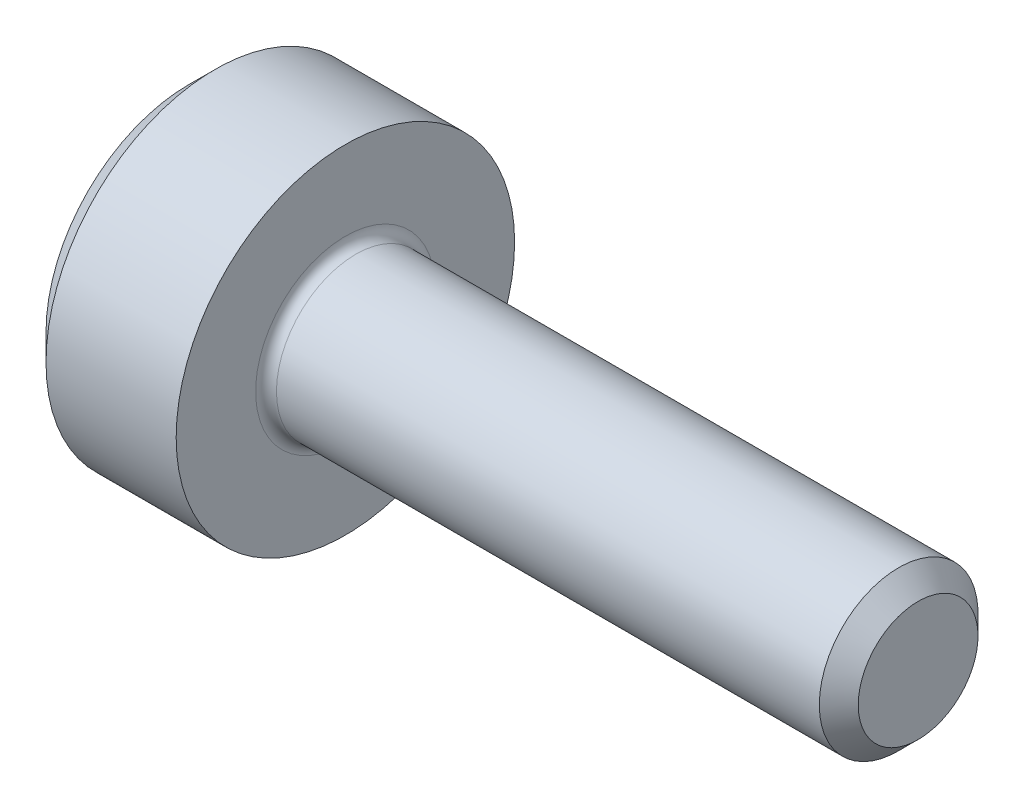
SolidWorks part; units mm, degrees
revolve "Base-Revolve" add sketch "BodySke"
sketch "BodySke" plane through (0, 0, 0) normal (0, 0, 1) x (1, 0, 0)
  line L0 (0, 0) -> (0, 2.75)
  line L1 (0.5, 3.25) -> (3, 3.25)
  line L2 (3, 3.25) -> (3, 1.524)
  line L3 (3, 1.524) -> (13.626, 1.524)
  line L4 (14, 1.15) -> (14, 0)
  line L5 (14, 0) -> (0, 0)
  line L6 (-31.75, 0) -> (127, 0) construction
  line L7 (0, 2.75) -> (0.5, 3.25)
  line L8 (14, 1.15) -> (13.626, 1.524)
  line L9 (0, -2.75) -> (0.5, -3.25) construction
  line L10 (14, -1.15) -> (13.626, -1.524) construction
  line L11 (3.8, 9.525) -> (3.8, 3.175) construction
  line L12 (6, 9.525) -> (6, 3.175) construction
  line L13 (-36, 9.525) -> (-36, 3.175) construction
  dimension "Diameter" = 3.048
  dimension "Head_ht" = 3
  dimension "Length" = 11
  dimension "Body_ch_ang" = 45
  dimension "Head_dia" = 6.5
  dimension "Head_ch_ang" = 45
  dimension "Minor_dia" = 2.3
  dimension "Advance" = 0.8
  dimension "Thread_nom" = 8
  dimension "Thread_length" = 50
  dimension "Head_ch_ht" = 0.5
cosmetic thread "ThreadCosmetic"
fillet "Fillet1" radius 0.2 1 edges at (3, 0, 1.524)
ref_plane "Plane1" through (0, 0, 0) normal (0, 0, 1) x (1, 0, 0)
ref_plane "Plane2" through (0, 0, 0) normal (0, 1, 0) x (1, 0, 0)
ref_plane "Plane3" through (0, 0, 0) normal (1, 0, 0) x (0, 0, -1)
sketch "Sketch2" plane through (0, 0, 0) normal (0, 0, 1) x (1, 0, 0)
  line L0 (0, 1.6) -> (2.5, 1.6)
  line L1 (2.5, 1.6) -> (3.4238, 0)
  line L2 (-31.75, 0) -> (127, 0) construction
  line L3 (3.4238, 0) -> (0, 0)
  line L4 (0, 0) -> (0, 1.6)
  line L5 (0, 2.75) -> (0, -2.75) construction
  line L6 (0, 0) -> (47.625, 0) construction
  line L7 (3, -3.25) -> (3, 3.25) construction
  dimension "D1" = 1.6
  dimension "D2" = 60
revolve "Hex-PreBroach" cut sketch "Sketch2" angle 360 about L6
sketch "Sketch3" plane through (0, 0, 0) normal (-1, 0, 0) x (0, 0.5, 0.866)
  line L0 (0.9238, 1.6) -> (-0.9238, 1.6)
  line L1 (-0.9238, 1.6) -> (-1.8475, 0)
  line L2 (0.9238, 1.6) -> (1.8475, 0)
  line L3 (0.9238, -1.6) -> (1.8475, 0)
  line L4 (0.9238, -1.6) -> (-0.9238, -1.6)
  line L5 (-0.9238, -1.6) -> (-1.8475, 0)
  dimension "D1" = 1.6
  dimension "D2" = 1.6
  dimension "Hex_size" = 3.2
extrude "Hex" cut sketch "Sketch3" against normal blind 2.5
sketch "Sketch4" plane through (0, 0, 0) normal (-1, 0, 0) x (0, 0, 1)
  line L0 (0, 0) -> (2.3876, 0)
  line L1 (0, 0) -> (6.1484, 3.5498) construction
  line L2 (0, 0) -> (1.1938, 2.0677)
  line L3 (1.9883, 0.576) -> (2.2704, 0.7389)
  line L4 (1.493, 1.4339) -> (1.7751, 1.5968)
  arc A0 (1.9883, 0.576) -> (1.493, 1.4339) centre (0, 0) ccw
  arc A1 (2.3876, 0) -> (2.2704, 0.7389) centre (0, 0) ccw
  arc A2 (1.1938, 2.0677) -> (1.7751, 1.5968) centre (0, 0) cw
  dimension "D1" = 30
  dimension "D2" = 60
  dimension "Spline_p_dim" = 0.9906
  dimension "D3" = 0.4953
extrude "Spline" [suppressed] cut sketch "Sketch4" against normal blind 2.5
pattern_circular "CirPattern1" [suppressed] count 6 every 60
sketch "Sketch5" plane through (0, 0, 0) normal (0, 0, 1) x (1, 0, 0)
  line L0 (-31.75, 0) -> (127, 0) construction
  line L2 (0, 2.75) -> (0, -2.75) construction
  circle A0 centre (2, 0) radius 0.675
  dimension "Drilled_hole_dia" = 1.35
  dimension "Drilled_hole_loc" = 2
extrude "Hole" [suppressed] cut sketch "Sketch5" against normal through all and the other way through all
pattern_circular "Drilled-4" [suppressed] count 2 every 60
pattern_circular "Drilled-6" [suppressed] count 3 every 60
sketch "ThdSchSke" plane through (0, 0, 0) normal (0, 0, 1) x (1, 0, 0)
  line L0 (6, -1.15) -> (5.7381, -1.524)
  line L1 (6, -1.15) -> (6.2619, -1.524)
  line L2 (6.2619, -1.524) -> (6.2619, -1.905)
  line L3 (-3.175, 0) -> (5.1513, 0) construction
  line L5 (6.2619, -1.905) -> (5.7381, -1.905)
  line L6 (5.7381, -1.905) -> (5.7381, -1.524)
  line L7 (0, 2.75) -> (0, -2.75) construction
  dimension "Thread_minor" = 2.3
  dimension "Diameter" = 3.048
  dimension "Start" = 6
revolve "ThreadSchematic" [suppressed] cut sketch "ThdSchSke" angle 360 about L3
pattern_linear "ThdSchPat" [suppressed]
equation "\"D2@Sketch3\" = \"Hex_size@Sketch3\" / 2"
equation "\"D1@Sketch3\" = \"Hex_size@Sketch3\" / 2"
equation "\"D1@Sketch2\" = \"Hex_size@Sketch3\" / 2"
equation "\"D3@Sketch4\" = \"Spline_p_dim@Sketch4\" / 2"
equation "\"Thread_minor@ThreadCosmetic\"  =  \"Minor_dia@BodySke\""
equation "\"D2@CirPattern1\" = 360 / \"Num_teeth@CirPattern1\""
equation "\"Wall_thickness@Sketch2\" = \"Head_ht@BodySke\" - \"Key_eng@Hex\""
equation "\"Thread_length@ThreadCosmetic\" = ((sgn( (\"Length@BodySke\" - \"Advance@BodySke\" ) - \"Thread_nom@BodySke\" )-1)*( (\"Length@BodySke\" - \"Advance@BodySke\" ) - \"Thread_nom@BodySke\" ))/-2+ \"Thread_nom@BodySke\""
equation "\"Thread_minor@ThdSchSke\" = \"Minor_dia@BodySke\""
equation "\"Diameter@ThdSchSke\" = \"Diameter@BodySke\""
equation "\"Overcut@ThdSchSke\" = \"Diameter@BodySke\" * 1.25"
equation "\"Start@ThdSchSke\" = \"Head_ht@BodySke\" + \"Length@BodySke\" - \"Thread_length@ThreadCosmetic\"  '---Non-countersunk---"
equation "\"Num_threads@ThdSchPat\" = int( \"Thread_length@ThreadCosmetic\" / \"Advance@BodySke\" + 0.999 )  + 1"
equation "\"Advance@ThdSchPat\" = \"Thread_length@ThreadCosmetic\" /  (\"Num_threads@ThdSchPat\" - 1) 'relax it"
equation "\"Num_threads@ThdSchPat\" = \"Num_threads@ThdSchPat\" - sgn( \"Num_threads@ThdSchPat\" - 1) '---chamfered tips only---"
